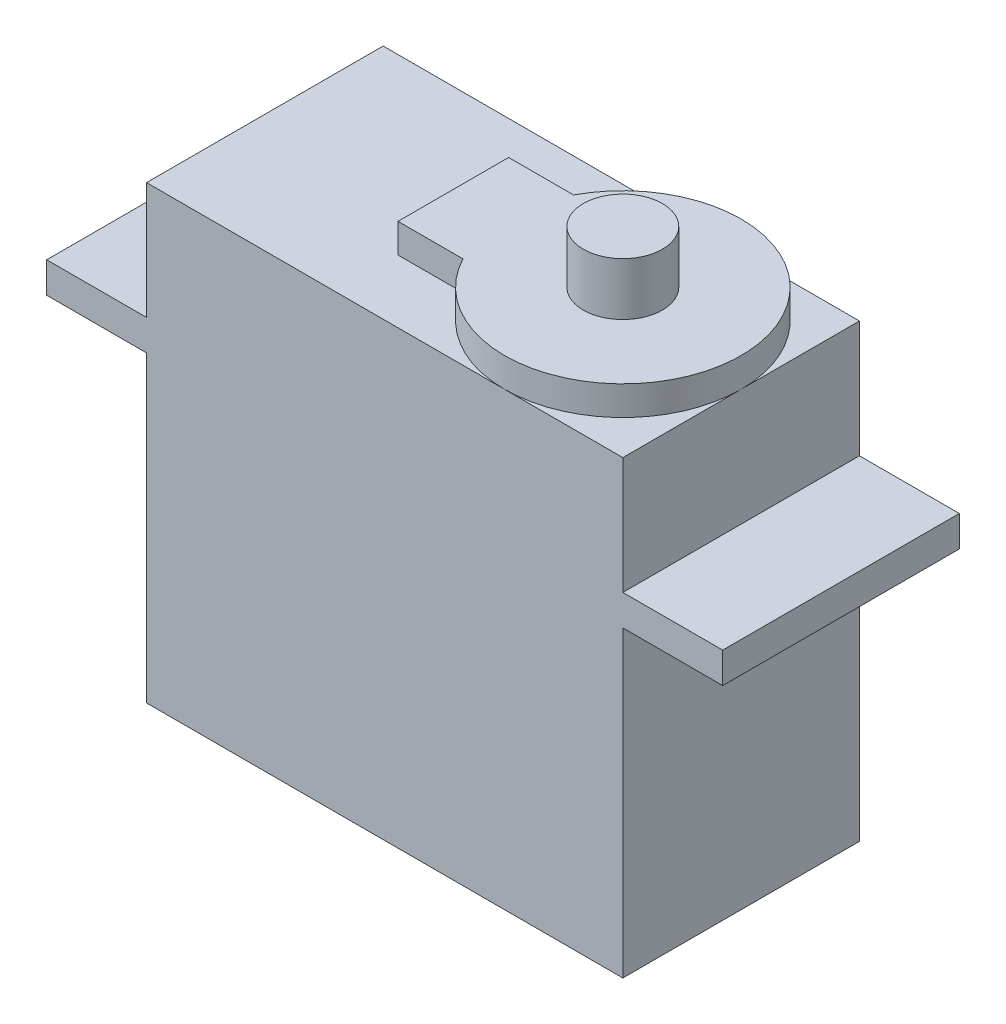
SolidWorks part; units mm, degrees
ref_plane "Front Plane" through (0, 0, 0) normal (0, 0, 1) x (1, 0, 0)
ref_plane "Top Plane" through (0, 0, 0) normal (0, 1, 0) x (1, 0, 0)
ref_plane "Right Plane" through (0, 0, 0) normal (1, 0, 0) x (0, 0, -1)
sketch "Sketch1" plane through (0, 0, 0) normal (0, 0, 1) x (1, 0, 0)
  line L1 (-11.811, 11.176) -> (11.811, 11.176)
  line L2 (-11.811, 11.176) -> (-11.811, -11.176)
  line L3 (-11.811, -11.176) -> (11.811, -11.176)
  line L4 (11.811, 11.176) -> (11.811, -11.176)
  line L5 (-11.811, 11.176) -> (11.811, -11.176) construction
  line L6 (-11.811, -11.176) -> (11.811, 11.176) construction
  point P0 (0, 0)
  dimension "D1" = 23.622
  dimension "D2" = 22.352
extrude "Boss-Extrude1" add sketch "Sketch1" along normal mid plane 11.7348
sketch "Sketch3" plane through (0, 0, 5.8674) normal (0, 0, 1) x (1, 0, 0)
  line L0 (-11.811, 11.176) -> (-11.811, -11.176) construction
  line L1 (-11.811, 5.3848) -> (-16.764, 5.3848)
  line L2 (-11.811, 5.3848) -> (-11.811, 3.8608)
  line L3 (-11.811, 3.8608) -> (-16.764, 3.8608)
  line L4 (-16.764, 5.3848) -> (-16.764, 3.8608)
  line L5 (0, 0) -> (0, 4.8904) construction
  line L6 (-11.811, -11.176) -> (11.811, -11.176) construction
  line L7 (16.764, 5.3848) -> (16.764, 3.8608)
  line L8 (11.811, 3.8608) -> (16.764, 3.8608)
  line L9 (11.811, 5.3848) -> (11.811, 3.8608)
  line L10 (11.811, 5.3848) -> (16.764, 5.3848)
  dimension "D1" = 1.524
  dimension "D2" = 33.528
  dimension "D3" = 15.0368
extrude "Boss-Extrude2" add sketch "Sketch3" against normal up to surface (11.7348 mm away) up to face at (0, 0, -5.8674)
sketch "Sketch4" plane through (0, 11.176, 0) normal (0, 1, 0) x (1, 0, 0)
  line L0 (11.811, 5.8674) -> (11.811, -5.8674) construction
  line L1 (11.811, -5.8674) -> (-11.811, -5.8674) construction
  line L2 (11.811, 5.8674) -> (-11.811, 5.8674) construction
  circle A0 centre (5.9436, 0) radius 5.8674
extrude "Boss-Extrude3" add sketch "Sketch4" along normal offset from surface (1.4478 mm away) 23.7998 up to face at (0, -11.176, 0)
sketch "Sketch5" plane through (0, 12.6238, 0) normal (0, 1, 0) x (1, 0, 0)
  circle A0 centre (5.9436, 0) radius 1.9621
  dimension "D1" = 3.9243
extrude "Boss-Extrude4" add sketch "Sketch5" along normal offset from surface (2.6162 mm away) 26.416 up to face at (0, -11.176, 0)
sketch "Sketch6" plane through (0, 12.6238, 0) normal (0, 1, 0) x (1, 0, 0)
  line L1 (0.757, 2.7432) -> (-2.4638, 2.7432)
  line L2 (0.757, 2.7432) -> (0.757, -2.7432)
  line L3 (0.757, -2.7432) -> (-2.4638, -2.7432)
  line L4 (-2.4638, 2.7432) -> (-2.4638, -2.7432)
  arc A0 (5.9436, 5.8674) -> (5.9436, -5.8674) centre (5.9436, 0) ccw construction
  arc A1 (11.811, 0) -> (5.9436, 5.8674) centre (5.9436, 0) ccw construction
  point P10 (-2.4638, 0)
  dimension "D1" = 14.2748
  dimension "D2" = 5.4864
extrude "Boss-Extrude5" add sketch "Sketch6" against normal up to surface (1.4478 mm away) up to face at (10.2603, 11.176, 4.3167)
